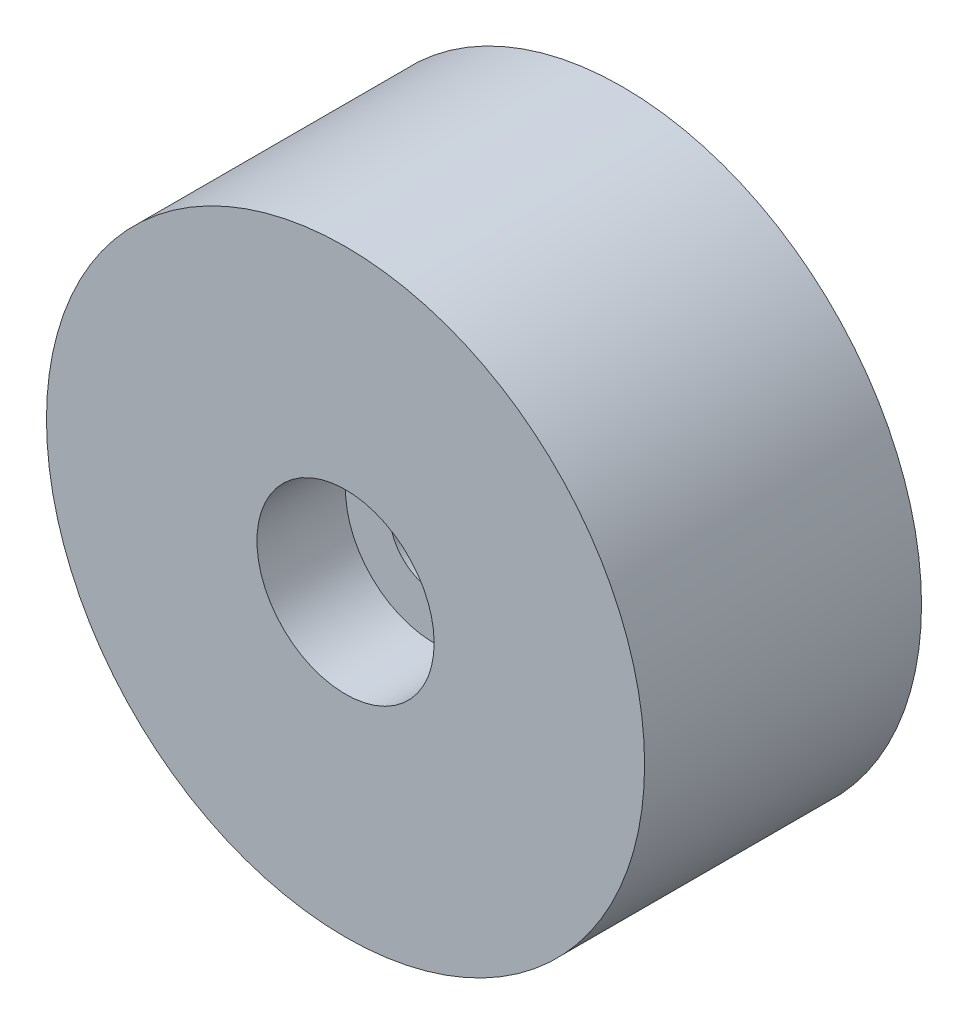
SolidWorks part; units mm, degrees
ref_plane "Front" through (0, 0, 0) normal (0, 0, 1) x (1, 0, 0)
ref_plane "Top" through (0, 0, 0) normal (0, 1, 0) x (1, 0, 0)
ref_plane "Right" through (0, 0, 0) normal (1, 0, 0) x (0, 0, -1)
sketch "Esquisse1" plane through (0, 0, 0) normal (0, 0, 1) x (1, 0, 0)
  circle A0 centre (0, 0) radius 27
  dimension "D1" = 54
extrude "Boss.-Extru.1" add sketch "Esquisse1" along normal blind 25
sketch "Esquisse2" plane through (0, 0, 25) normal (0, 0, 1) x (1, 0, 0)
  circle A0 centre (0, 0) radius 8
  dimension "D1" = 16
extrude "Enlèv. mat.-Extru.1" cut sketch "Esquisse2" against normal blind 8
sketch "Esquisse3" plane through (0, 0, 17) normal (0, 0, 1) x (1, 0, 0)
  circle A0 centre (0, 0) radius 4
  dimension "D1" = 8
extrude "Enlèv. mat.-Extru.2" cut sketch "Esquisse3" against normal through all
